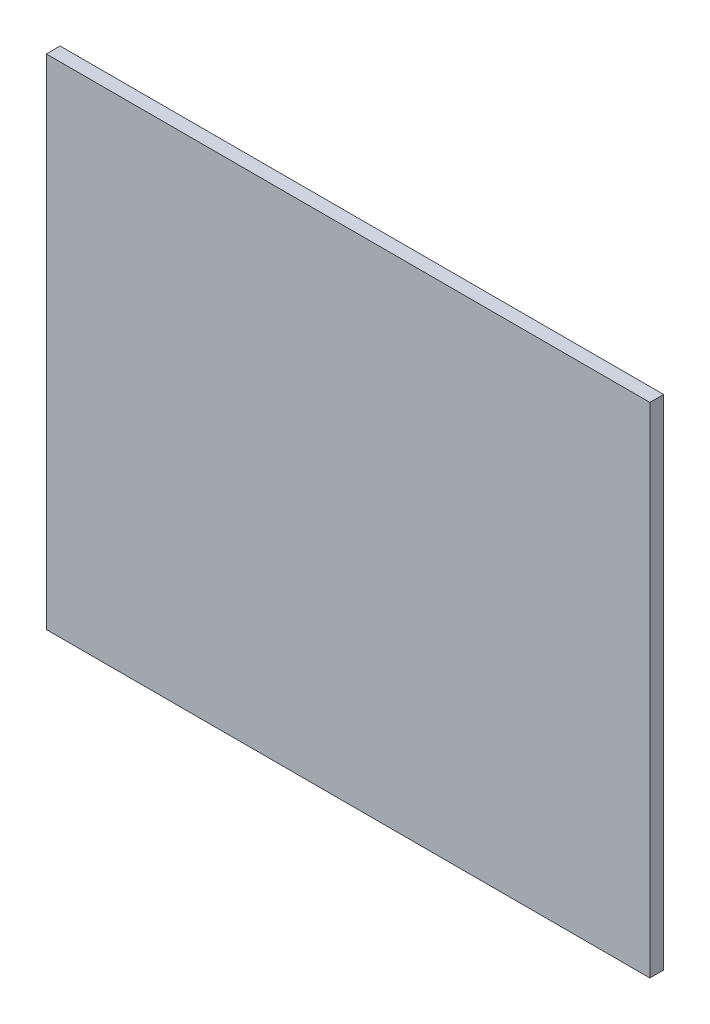
SolidWorks part; units mm, degrees
material "Acrylic (Medium-high impact)"
ref_plane "Front Plane" through (0, 0, 0) normal (0, 0, 1) x (1, 0, 0)
ref_plane "Top Plane" through (0, 0, 0) normal (0, 1, 0) x (1, 0, 0)
ref_plane "Right Plane" through (0, 0, 0) normal (1, 0, 0) x (0, 0, -1)
sketch "Sketch1" plane through (0, 0, 0) normal (0, 0, 1) x (1, 0, 0)
  line L0 (46.8271, -25.7711) -> (46.8271, 31.6329) construction
  line L1 (-22.6729, 31.6329) -> (46.8271, 31.6329)
  line L2 (-22.6729, 31.6329) -> (-22.6729, -25.7711)
  line L3 (-22.6729, -25.7711) -> (46.8271, -25.7711)
  line L4 (46.8271, 31.6329) -> (46.8271, -25.7711)
extrude "Boss-Extrude1" add sketch "Sketch1" along normal blind 1.5875
